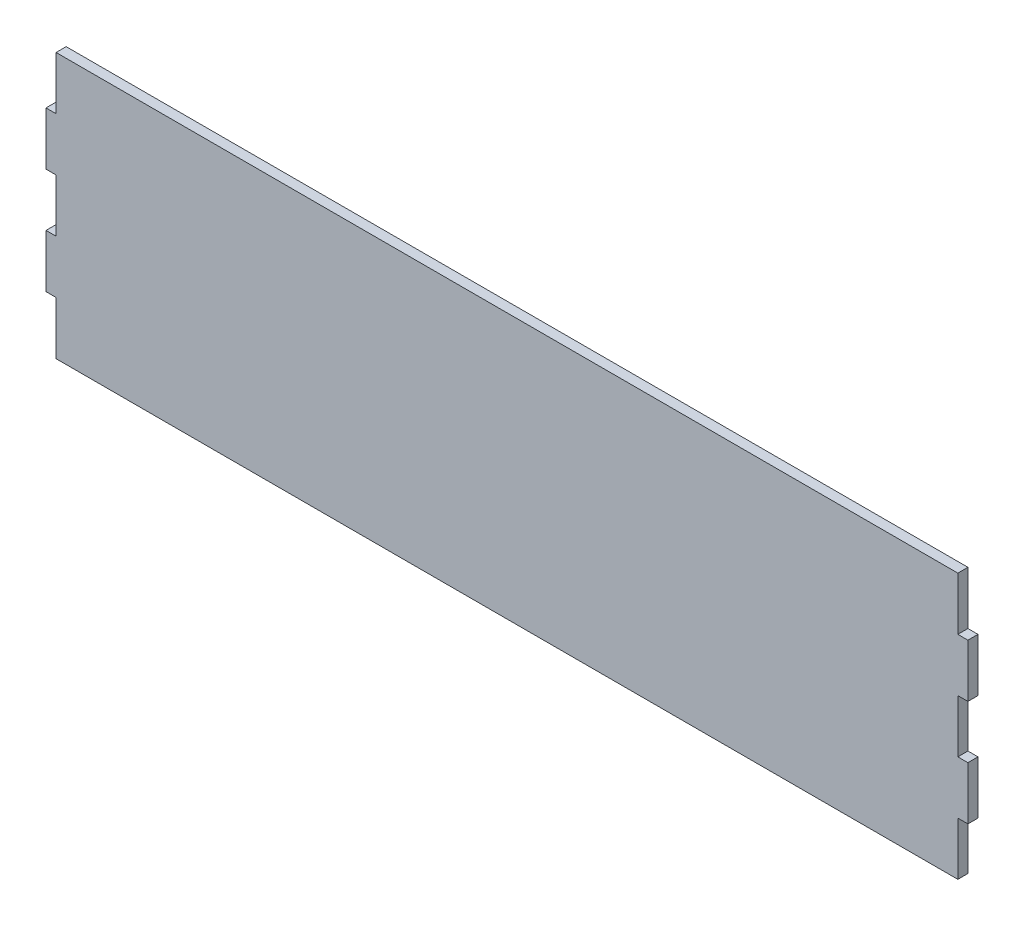
SolidWorks part; units mm, degrees
material "1060 Alloy"
ref_plane "Front Plane" through (0, 0, 0) normal (0, 0, 1) x (1, 0, 0)
ref_plane "Top Plane" through (0, 0, 0) normal (0, 1, 0) x (1, 0, 0)
ref_plane "Right Plane" through (0, 0, 0) normal (1, 0, 0) x (0, 0, -1)
sketch "Sketch1" plane through (0, 0, 0) normal (0, 0, 1) x (1, 0, 0)
  line L0 (0, 76.2) -> (0, 50.8)
  line L1 (0, 127) -> (431.8, 127)
  line L2 (0, 127) -> (0, 101.6)
  line L3 (0, 0) -> (431.8, 0)
  line L4 (431.8, 127) -> (431.8, 0) construction
  line L5 (0, 101.6) -> (-4.826, 101.6)
  line L6 (215.9, 127) -> (215.9, 0) construction
  line L7 (0, 76.2) -> (-4.826, 76.2)
  line L8 (-4.826, 101.6) -> (-4.826, 76.2)
  line L9 (0, 50.8) -> (-4.826, 50.8)
  line L10 (431.8, 25.4) -> (431.8, 0)
  line L11 (0, 25.4) -> (-4.826, 25.4)
  line L12 (-4.826, 50.8) -> (-4.826, 25.4)
  line L13 (0, 25.4) -> (0, 0)
  line L15 (431.8, 25.4) -> (436.626, 25.4)
  line L16 (436.626, 50.8) -> (436.626, 25.4)
  line L17 (431.8, 50.8) -> (436.626, 50.8)
  line L18 (431.8, 76.2) -> (431.8, 50.8)
  line L19 (431.8, 76.2) -> (436.626, 76.2)
  line L20 (436.626, 101.6) -> (436.626, 76.2)
  line L21 (431.8, 101.6) -> (436.626, 101.6)
  line L22 (431.8, 127) -> (431.8, 101.6)
  dimension "D1" = 127
  dimension "D2" = 431.8
  dimension "D3" = 4.826
extrude "Boss-Extrude1" add sketch "Sketch1" along normal blind 4.826
equation "\"w\"= .19"
equation "\"D3@Sketch1\"=\"w\""
equation "\"D1@Boss-Extrude1\"=\"w\""
